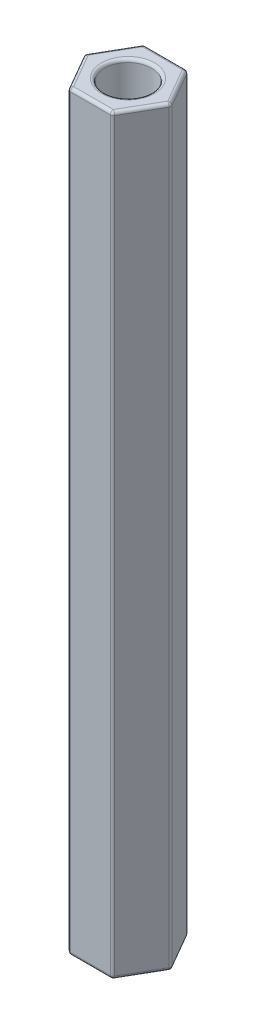
SolidWorks part; units mm, degrees
ref_plane "Front Plane" through (0, 0, 0) normal (0, 0, 1) x (1, 0, 0)
ref_plane "Top Plane" through (0, 0, 0) normal (0, 1, 0) x (1, 0, 0)
ref_plane "Right Plane" through (0, 0, 0) normal (1, 0, 0) x (0, 0, -1)
sketch "Sketch1" plane through (0, 0, 0) normal (0, 1, 0) x (1, 0, 0)
  line L1 (1.7321, 3) -> (-1.7321, 3)
  line L2 (-1.7321, 3) -> (-3.4641, 0)
  line L3 (-3.4641, 0) -> (-1.7321, -3)
  line L4 (-1.7321, -3) -> (1.7321, -3)
  line L5 (1.7321, -3) -> (3.4641, 0)
  line L6 (3.4641, 0) -> (1.7321, 3)
  circle A0 centre (0, 0) radius 3 construction
  circle A1 centre (0, 0) radius 1.875
  dimension "D1" = 6
  dimension "D2" = 3.75
extrude "Boss-Extrude1" add sketch "Sketch1" along normal mid plane 60
fillet "Fillet1" radius 0.25 20 edges at (2.5981, 30, 1.5) (2.5981, -30, 1.5) (3.4641, 0, 0) (2.5981, 30, -1.5) (2.5981, -30, -1.5) (1.7321, 0, -3) (0, 30, -3) (0, -30, -3) (-2.5981, 30, 1.5) (-2.5981, -30, 1.5) (-1.7321, 0, 3) (0, 30, 3) (1.7321, 0, 3) (0, -30, 3) (-1.7321, 0, -3) (-2.5981, 30, -1.5) (-3.4641, 0, 0) (-2.5981, -30, -1.5) (0, -30, 1.875) (0, 30, 1.875)
